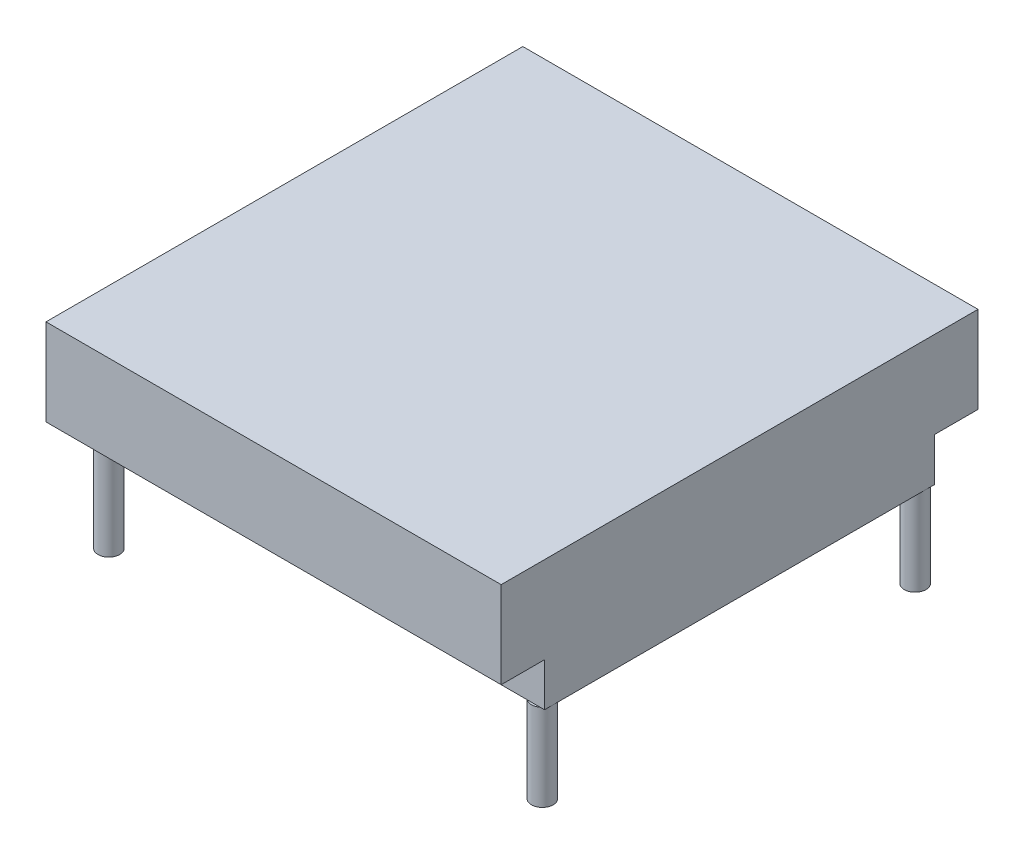
SolidWorks part; units mm, degrees
ref_plane "Front Plane" through (0, 0, 0) normal (0, 0, 1) x (1, 0, 0)
ref_plane "Top Plane" through (0, 0, 0) normal (0, 1, 0) x (1, 0, 0)
ref_plane "Right Plane" through (0, 0, 0) normal (1, 0, 0) x (0, 0, -1)
sketch "Sketch1" plane through (0, 0, 0) normal (0, 1, 0) x (1, 0, 0)
  line L1 (0, 111.8813) -> (133.35, 111.8813)
  line L2 (0, 111.8813) -> (0, -27.8187)
  line L3 (0, -27.8187) -> (133.35, -27.8187)
  line L4 (133.35, 111.8813) -> (133.35, -27.8187)
  dimension "D1" = 139.7
  dimension "D2" = 133.35
extrude "Boss-Extrude1" add sketch "Sketch1" along normal blind 25.4
sketch "Sketch2" plane through (0, 0, 0) normal (0, -1, 0) x (-1, 0, 0)
  line L0 (-133.35, -27.8187) -> (-133.35, 111.8813) construction
  line L1 (-133.35, -15.1187) -> (-82.55, -15.1187)
  line L2 (-133.35, -15.1187) -> (-133.35, 99.1813)
  line L3 (-133.35, 99.1813) -> (-82.55, 99.1813)
  line L4 (-82.55, -15.1187) -> (-82.55, 99.1813)
  dimension "D1" = 12.7
  dimension "D2" = 12.7
  dimension "D3" = 50.8
extrude "Boss-Extrude2" add sketch "Sketch2" along normal blind 12.7
sketch "Sketch3" plane through (0, 0, 0) normal (0, -1, 0) x (-1, 0, 0)
  line L0 (-133.35, 111.8813) -> (0, 111.8813) construction
  line L1 (0, 111.8813) -> (0, -27.8187) construction
  circle A0 centre (-3.175, 96.6413) radius 3.175
  dimension "D2" = 6.35
  dimension "D1" = 15.24
  dimension "D3" = 3.175
extrude "Boss-Extrude3" add sketch "Sketch3" along normal blind 38.1
sketch "Sketch4" plane through (0, 0, 0) normal (0, -1, 0) x (-1, 0, 0)
  line L0 (0, -27.8187) -> (-133.35, -27.8187) construction
  line L1 (0, 111.8813) -> (0, 96.6413) construction
  circle A0 centre (-3.175, -12.5787) radius 3.175
  dimension "D1" = 15.24
  dimension "D3" = 6.35
  dimension "D2" = 3.175
extrude "Boss-Extrude4" add sketch "Sketch4" along normal blind 38.1
sketch "Sketch5" plane through (0, -12.7, 0) normal (0, -1, 0) x (-1, 0, 0)
  line L0 (-133.35, 111.8813) -> (0, 111.8813) construction
  line L1 (-133.35, 99.1813) -> (-133.35, -15.1187) construction
  circle A1 centre (-130.175, 96.6413) radius 3.175
  dimension "D2" = 6.35
  dimension "D1" = 15.24
  dimension "D3" = 3.175
extrude "Boss-Extrude5" add sketch "Sketch5" along normal blind 25.4
sketch "Sketch6" plane through (0, -12.7, 0) normal (0, -1, 0) x (-1, 0, 0)
  line L0 (0, -27.8187) -> (-133.35, -27.8187) construction
  line L1 (-133.35, 99.1813) -> (-133.35, 96.6413) construction
  circle A0 centre (-130.175, -12.5787) radius 3.175
  dimension "D2" = 6.35
  dimension "D1" = 15.24
  dimension "D3" = 3.175
extrude "Boss-Extrude6" add sketch "Sketch6" along normal blind 25.4
